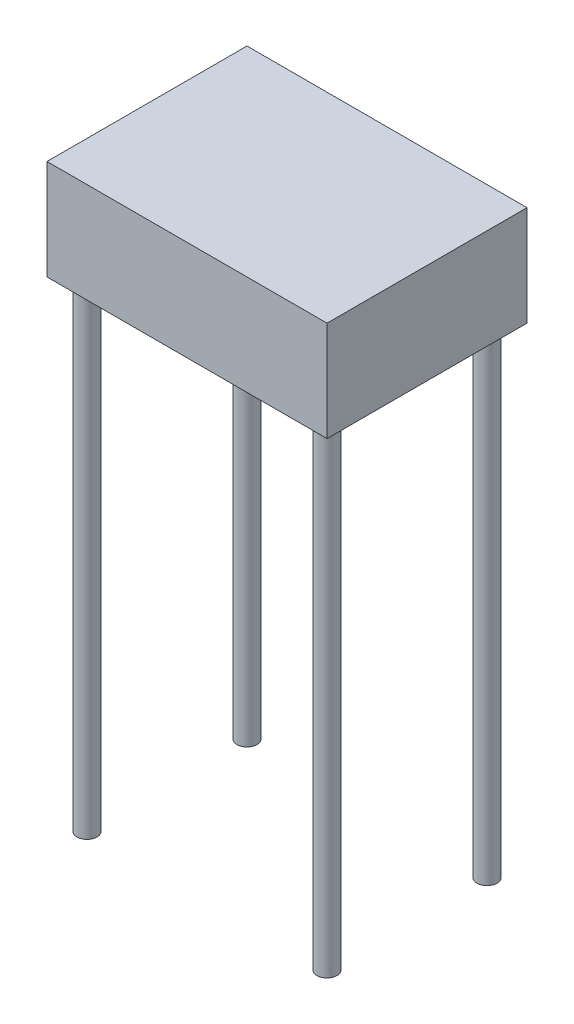
SolidWorks part; units mm, degrees
ref_plane "前视基准面" through (0, 0, 0) normal (0, 0, 1) x (1, 0, 0)
ref_plane "上视基准面" through (0, 0, 0) normal (0, 1, 0) x (1, 0, 0)
ref_plane "右视基准面" through (0, 0, 0) normal (1, 0, 0) x (0, 0, -1)
sketch "草图1" plane through (0, 0, 0) normal (0, 1, 0) x (1, 0, 0)
  line L1 (-300, 200) -> (300, 200) construction
  line L2 (-300, 200) -> (-300, -200) construction
  line L3 (-300, -200) -> (300, -200) construction
  line L4 (300, 200) -> (300, -200) construction
  line L5 (-300, 200) -> (300, -200) construction
  line L6 (-300, -200) -> (300, 200) construction
  circle A0 centre (-300, 200) radius 25
  circle A1 centre (300, 200) radius 25
  circle A2 centre (300, -200) radius 25
  circle A3 centre (-300, -200) radius 25
  point P0 (0, 0)
  dimension "D3" = 50
  dimension "D1" = 600
  dimension "D2" = 400
extrude "凸台-拉伸1" add sketch "草图1" along normal blind 1200
sketch "草图2" plane through (0, 1200, 0) normal (0, 1, 0) x (1, 0, 0)
  line L1 (-350, 250) -> (350, 250)
  line L2 (-350, 250) -> (-350, -250)
  line L3 (-350, -250) -> (350, -250)
  line L4 (350, 250) -> (350, -250)
  line L5 (-350, 250) -> (350, -250) construction
  line L6 (-350, -250) -> (350, 250) construction
  point P0 (0, 0)
  dimension "D1" = 700
  dimension "D2" = 500
extrude "凸台-拉伸2" add sketch "草图2" along normal blind 250
